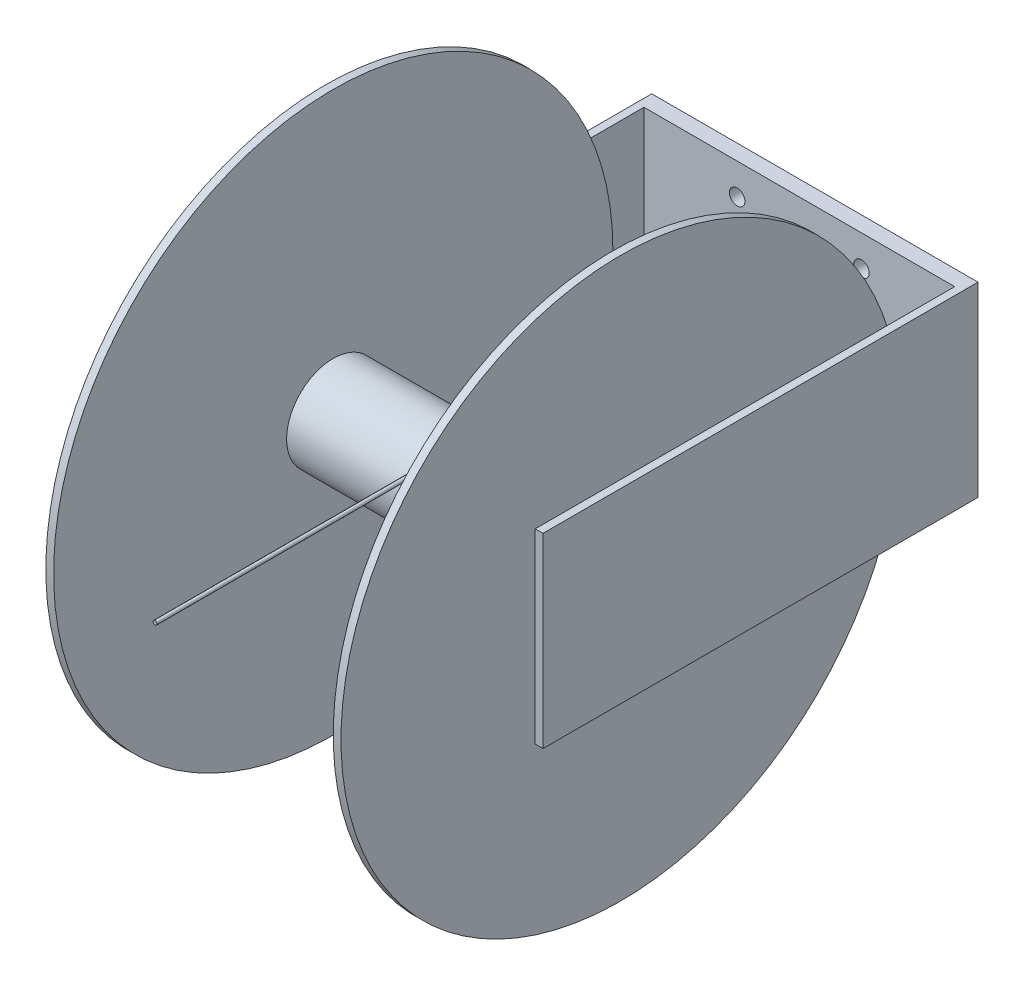
SolidWorks part; units mm, degrees
material "1060 Alloy"
ref_plane "Front Plane" through (0, 0, 0) normal (0, 0, 1) x (1, 0, 0)
ref_plane "Top Plane" through (0, 0, 0) normal (0, 1, 0) x (1, 0, 0)
ref_plane "Right Plane" through (0, 0, 0) normal (1, 0, 0) x (0, 0, -1)
sketch "Sketch1" plane through (0, 0, 0) normal (1, 0, 0) x (0, 0, -1)
  circle A0 centre (0, 0) radius 228.6
  dimension "D1" = 457.2
extrude "Boss-Extrude1" add sketch "Sketch1" along normal blind 6.35
sketch "Sketch2" plane through (6.35, 0, 0) normal (1, 0, 0) x (0, 0, -1)
  circle A0 centre (0, 0) radius 38.1
extrude "Boss-Extrude2" add sketch "Sketch2" along normal blind 228.6
sketch "Sketch3" plane through (234.95, 0, 0) normal (1, 0, 0) x (0, 0, -1)
  circle A0 centre (0, 0) radius 228.6
  dimension "D1" = 457.2
extrude "Boss-Extrude3" add sketch "Sketch3" along normal blind 6.35
sketch "Sketch4" plane through (241.3, 0, 0) normal (1, 0, 0) x (0, 0, -1)
  circle A0 centre (0, 0) radius 38.1
  dimension "D1" = 76.2
extrude "Boss-Extrude4" add sketch "Sketch4" along normal blind 6.35
sketch "Sketch5" plane through (0, 0, 0) normal (-1, 0, 0) x (0, 0, 1)
  circle A0 centre (0, 0) radius 38.1
  dimension "D1" = 76.2
extrude "Boss-Extrude5" add sketch "Sketch5" along normal blind 6.35
sketch "Sketch6" plane through (247.65, 0, 0) normal (1, 0, 0) x (0, 0, -1)
  line L4 (-76.2, -76.2) -> (-76.2, 0)
  line L13 (-5.0285, 76.2) -> (76.2, 76.2)
  line L20 (76.2, 76.2) -> (76.2, -76.2)
  line L21 (-5.0285, 76.2) -> (-76.2, 76.2)
  line L22 (-76.2, 76.2) -> (-76.2, 0)
  line L29 (76.2, -76.2) -> (-76.2, -76.2)
  dimension "D2" = 152.4
  dimension "D3" = 152.4
extrude "Boss-Extrude6" add sketch "Sketch6" along normal blind 6.35
sketch "Sketch7" plane through (254, 0, 0) normal (1, 0, 0) x (0, 0, -1)
  line L0 (76.2, 76.2) -> (76.2, -76.2)
  line L1 (76.2, 76.2) -> (279.4, 76.2)
  line L2 (76.2, -76.2) -> (279.4, -76.2)
  line L3 (279.4, 76.2) -> (279.4, -76.2)
  dimension "D1" = 203.2
extrude "Boss-Extrude7" add sketch "Sketch7" against normal blind 6.35
sketch "Sketch8" plane through (-6.35, 0, 0) normal (-1, 0, 0) x (0, 0, 1)
  line L1 (-76.2, -76.2) -> (76.2, -76.2)
  line L3 (-76.2, 76.2) -> (76.2, 76.2)
  line L4 (76.2, -76.2) -> (76.2, 76.2)
  line L5 (-76.2, -76.2) -> (76.2, 76.2) construction
  line L6 (-76.2, 76.2) -> (76.2, -76.2) construction
  line L7 (-76.2, 76.2) -> (-279.4, 76.2)
  line L8 (-76.2, -76.2) -> (-279.4, -76.2)
  line L9 (-279.4, 76.2) -> (-279.4, -76.2)
  point P0 (0, 0)
  dimension "D1" = 152.4
  dimension "D2" = 152.4
  dimension "D3" = 203.2
extrude "Boss-Extrude8" add sketch "Sketch8" along normal blind 6.35
sketch "Sketch9" plane through (247.65, 0, 0) normal (-1, 0, 0) x (0, 0, 1)
  line L0 (-279.4, 76.2) -> (-266.7, 76.2)
  line L1 (-279.4, 76.2) -> (-279.4, -75.4351)
  line L2 (-266.7, 76.2) -> (-266.7, -75.4351)
  line L3 (-279.4, -75.4351) -> (-266.7, -75.4351)
  line L4 (-279.4, 76.2) -> (76.2, 76.2) construction
  dimension "D1" = 12.7
extrude "Boss-Extrude9" add sketch "Sketch9" along normal up to surface (254 mm away) up to face at (-6.35, 0, 38.1)
sketch "Sketch10" plane through (0, 0, -279.4) normal (0, 0, -1) x (-1, 0, 0)
  line L0 (12.7, 76.2) -> (-254, 76.2) construction
  line L1 (-120.65, 76.2) -> (-120.65, -75.4351) construction
  line L2 (6.35, -75.4351) -> (-247.65, -75.4351) construction
  circle A0 centre (-171.45, 50.8) radius 6.35
  circle A1 centre (-69.85, 50.8) radius 6.35
  circle A2 centre (-69.85, -50.8) radius 6.35
  circle A3 centre (-171.45, -50.8) radius 6.35
  dimension "D1" = 12.7
  dimension "D2" = 25.4
  dimension "D5" = 50.8
  dimension "D3" = 2
  dimension "D4" = 2
extrude "Cut-Extrude1" cut sketch "Sketch10" against normal up to surface (12.7 mm away) up to face at (120.65, 0.3824, -266.7)
ref_plane "Plane1" through (120.65, 0, 0) normal (-1, 0, 0) x (0, 0, 1)
sketch "Sketch12" plane through (120.65, 0, 0) normal (-1, 0, 0) x (0, 0, 1)
  line L5 (0, 38.1) -> (260, 38.1)
  line L6 (0, 0) -> (260, 0) construction
  line L7 (260, 0) -> (260, 38.1) construction
  line L8 (0, 0) -> (-38.1, 0) construction
  arc A1 (-38.1, 0) -> (0, 38.1) centre (0, 0) cw
  dimension "D1" = 260
sketch "Sketch13" plane through (0, 0, 0) normal (0, 1, 0) x (1, 0, 0)
  line L0 (234.95, 38.1) -> (6.35, 38.1) construction
  circle A1 centre (120.65, 38.1) radius 1.59
  dimension "D1" = 3.18
sweep "Sweep1" add profiles "Sketch13" path "Sketch12"
